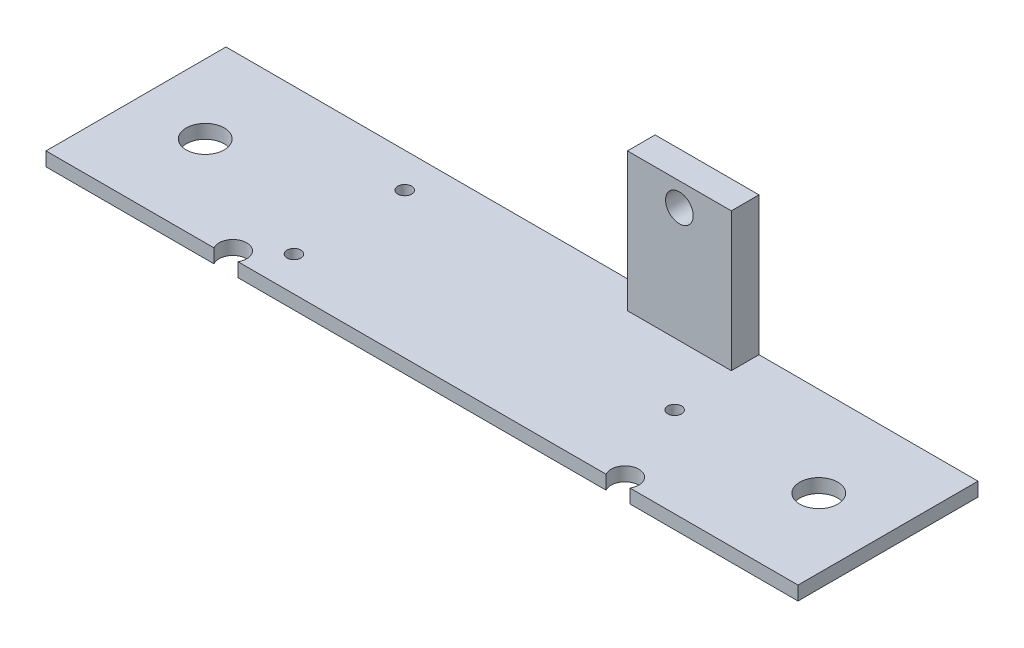
SolidWorks part; units mm, degrees
ref_plane "Front Plane" through (0, 0, 0) normal (0, 0, 1) x (1, 0, 0)
ref_plane "Top Plane" through (0, 0, 0) normal (0, 1, 0) x (1, 0, 0)
ref_plane "Right Plane" through (0, 0, 0) normal (1, 0, 0) x (0, 0, -1)
sketch "Sketch1" plane through (0, 0, 0) normal (0, 1, 0) x (1, 0, 0)
  line L0 (-108.64, -13) -> (0, -13) construction
  line L1 (0, 0) -> (-108.64, 0)
  line L2 (0, 0) -> (0, -26)
  line L3 (0, -26) -> (-108.64, -26)
  line L4 (-108.64, 0) -> (-108.64, -26)
  line L5 (-54.32, -26) -> (-54.32, 0) construction
  line L7 (-32.8062, 0) -> (-47.8062, 0)
  circle A0 centre (-98.64, -13) radius 2.75
  circle A1 centre (-10, -13) radius 2.75
  circle A2 centre (-26, -25) radius 2
  circle A3 centre (-82.64, -25) radius 2
  circle A4 centre (-30.82, -13) radius 1
  circle A5 centre (-77.82, -21) radius 1
  circle A6 centre (-77.82, -5) radius 1
  dimension "D3" = 5.5
  dimension "D5" = 5.5
  dimension "D6" = 10
  dimension "D7" = 4
  dimension "D10" = 4
  dimension "D12" = 2
  dimension "D14" = 2
  dimension "D15" = 2
  dimension "D1" = 108.64
  dimension "D2" = 26
  dimension "D4" = 10
  dimension "D8" = 26
  dimension "D9" = 1
  dimension "D11" = 26
  dimension "D13" = 30.82
  dimension "D16" = 47
  dimension "D17" = 47
  dimension "D18" = 16
  dimension "D19" = 8
extrude "Boss-Extrude1" add sketch "Sketch1" along normal blind 2 contours A3 L3 A2 L2 L1 L4 A6 A5 A4 A1 A0
sketch "Sketch2" plane through (0, 2, 0) normal (0, 1, 0) x (1, 0, 0)
  line L0 (0, 0) -> (-108.64, 0) construction
  line L1 (-31.6384, 0) -> (-46.6384, 0)
  line L2 (-31.6384, 0) -> (-31.6384, -4)
  line L3 (-31.6384, -4) -> (-46.6384, -4)
  line L4 (-46.6384, 0) -> (-46.6384, -4)
  dimension "D1" = 15
  dimension "D2" = 4
extrude "Boss-Extrude2" add sketch "Sketch2" along normal blind 20
sketch "Sketch3" plane through (0, 0, 4) normal (0, 0, 1) x (1, 0, 0)
  line L0 (-39.1384, 22) -> (-39.1384, 2) construction
  line L1 (-46.6384, 22) -> (-31.6384, 22) construction
  line L2 (-46.6384, 2) -> (-31.6384, 2) construction
  circle A0 centre (-39.1384, 18.6227) radius 2
  dimension "D1" = 4
extrude "Cut-Extrude1" cut sketch "Sketch3" against normal blind 20
